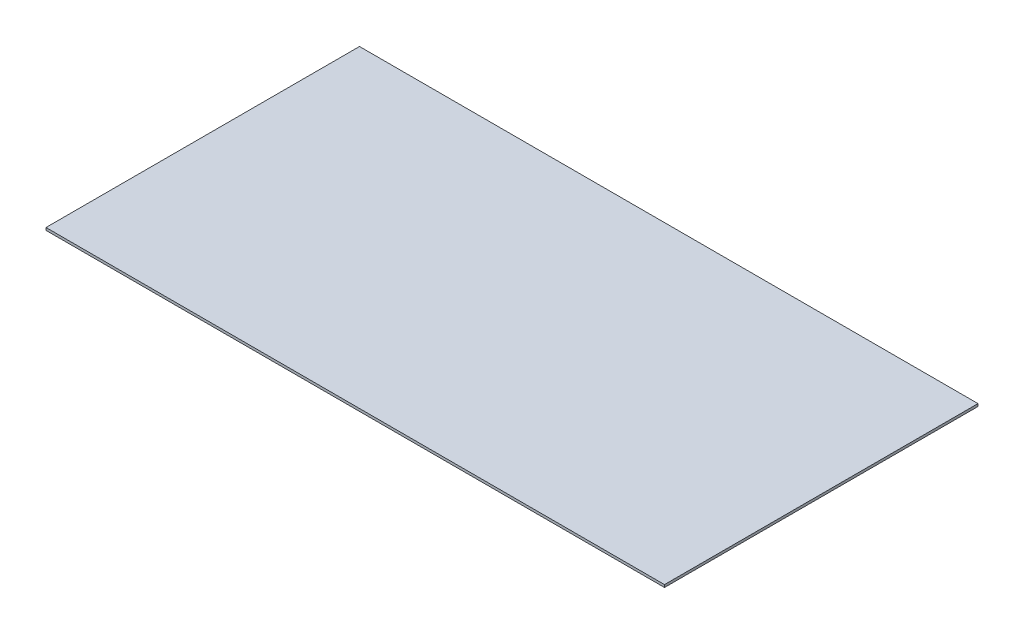
SolidWorks part; units mm, degrees
material "PPE"
ref_plane "Front Plane" through (0, 0, 0) normal (0, 0, 1) x (1, 0, 0)
ref_plane "Top Plane" through (0, 0, 0) normal (0, 1, 0) x (1, 0, 0)
ref_plane "Right Plane" through (0, 0, 0) normal (1, 0, 0) x (0, 0, -1)
sketch "Sketch1" plane through (0, 0, 0) normal (0, 1, 0) x (1, 0, 0)
  line L1 (-365, -185) -> (365, -185)
  line L2 (-365, -185) -> (-365, 185)
  line L3 (-365, 185) -> (365, 185)
  line L4 (365, -185) -> (365, 185)
  line L5 (-365, -185) -> (365, 185) construction
  line L6 (-365, 185) -> (365, -185) construction
  point P0 (0, 0)
  dimension "D1" = 730
  dimension "D2" = 370
extrude "Boss-Extrude1" add sketch "Sketch1" along normal blind 3
